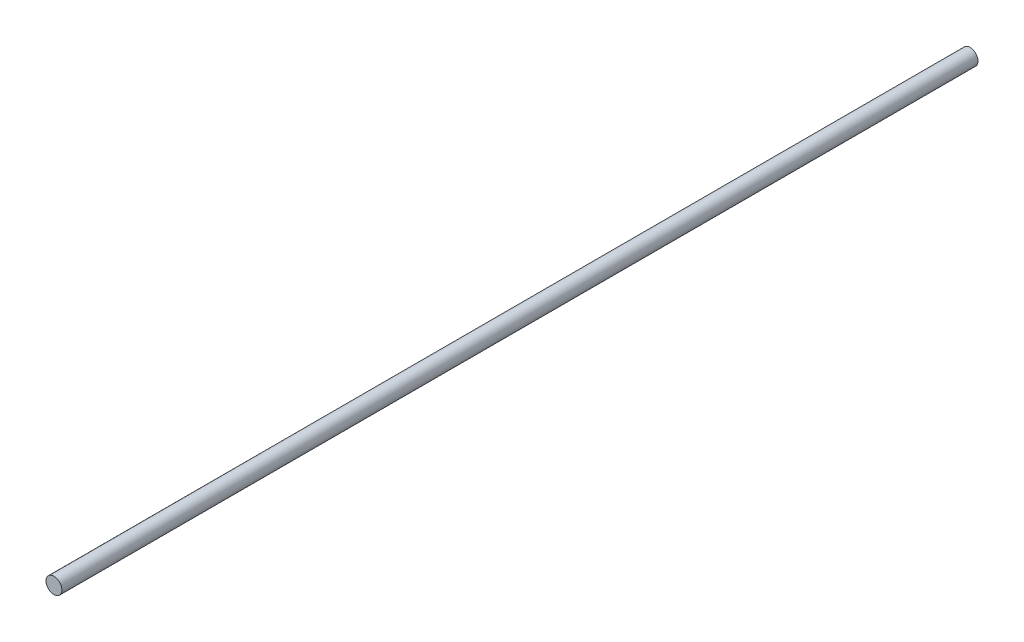
SolidWorks part; units mm, degrees
ref_plane "Front Plane" through (0, 0, 0) normal (0, 0, 1) x (1, 0, 0)
ref_plane "Top Plane" through (0, 0, 0) normal (0, 1, 0) x (1, 0, 0)
ref_plane "Right Plane" through (0, 0, 0) normal (1, 0, 0) x (0, 0, -1)
sketch "Sketch1" plane through (0, 0, 0) normal (0, 0, 1) x (1, 0, 0)
  circle A0 centre (0, 0) radius 0.65
  dimension "D1" = 1.3
extrude "Boss-Extrude1" add sketch "Sketch1" along normal blind 75
